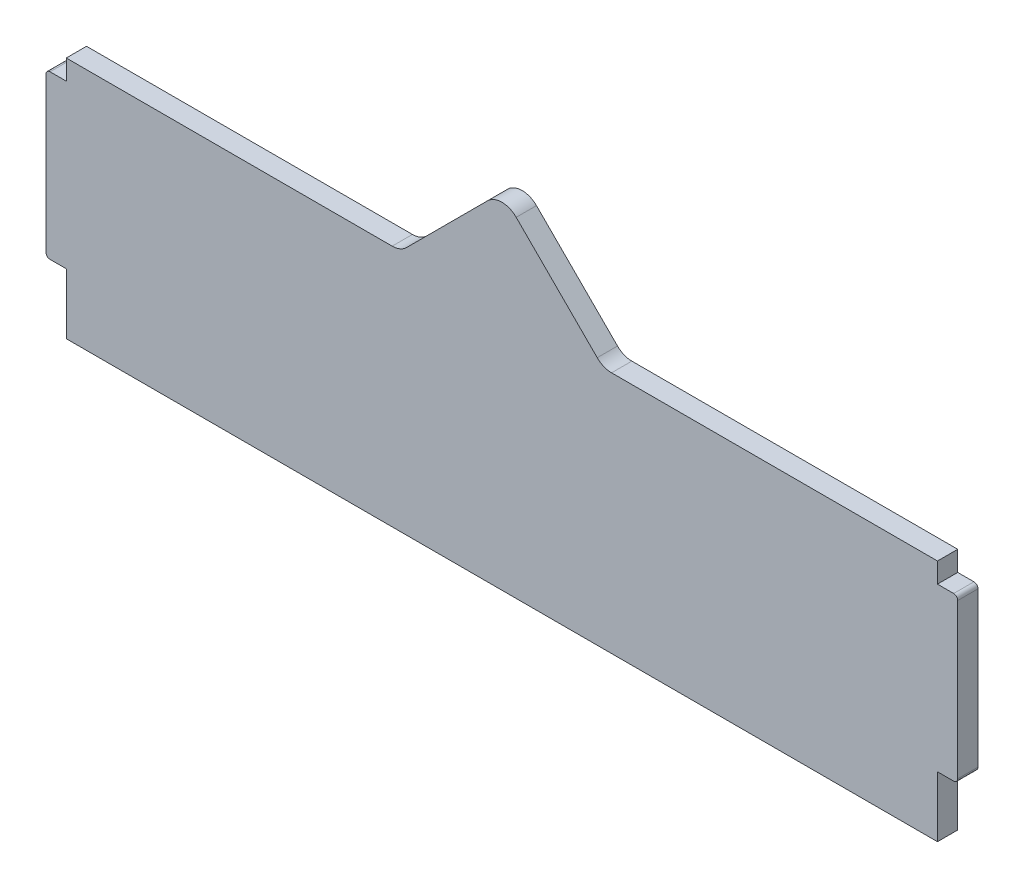
SolidWorks part; units mm, degrees
ref_plane "Front" through (0, 0, 0) normal (0, 0, 1) x (1, 0, 0)
ref_plane "Top" through (0, 0, 0) normal (0, 1, 0) x (1, 0, 0)
ref_plane "Right" through (0, 0, 0) normal (1, 0, 0) x (0, 0, -1)
sketch "Sketch1" plane through (0, 0, 0) normal (0, 0, 1) x (1, 0, 0)
  line L0 (215, 55.05) -> (215, 60)
  line L1 (0, 0) -> (215, 0)
  line L2 (0, 0) -> (0, 14.95)
  line L3 (0, 60) -> (82.5, 60)
  line L4 (215, 0) -> (215, 14.95)
  line L5 (0, 55.05) -> (-5, 55.05)
  line L7 (0, 14.95) -> (-5, 14.95)
  line L8 (-5, 55.05) -> (-5, 14.95)
  line L9 (215, 55.05) -> (220, 55.05)
  line L11 (215, 14.95) -> (220, 14.95)
  line L12 (220, 55.05) -> (220, 14.95)
  line L13 (0, 55.05) -> (0, 60)
  line L14 (82.5, 60) -> (107.5, 85)
  line L15 (107.5, 85) -> (132.5, 60)
  line L16 (132.5, 60) -> (215, 60)
  dimension "D1" = 215
  dimension "D2" = 60
  dimension "D3" = 5
  dimension "D4" = 4.95
  dimension "D5" = 40.1
  dimension "D6" = 4.95
  dimension "D7" = 40.1
  dimension "D8" = 5
  dimension "D9" = 25
  dimension "D10" = 25
  dimension "D11" = 107.5
extrude "Boss-Extrude1" add sketch "Sketch1" along normal blind 5
fillet "Fillet1" radius 5 3 edges at (82.5, 60, 2.5) (132.5, 60, 2.5) (107.5, 85, 2.5)
fillet "Fillet2" radius 1 4 edges at (-5, 55.05, 2.5) (-5, 14.95, 2.5) (220, 14.95, 2.5) (220, 55.05, 2.5)
